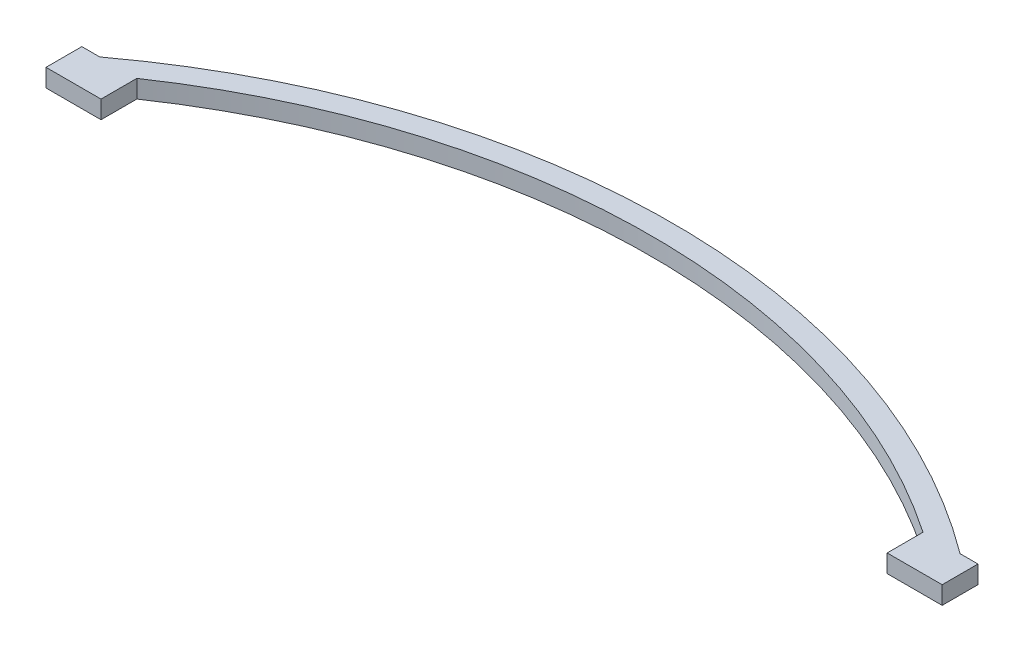
SolidWorks part; units mm, degrees
ref_plane "Front" through (0, 0, 0) normal (0, 0, 1) x (1, 0, 0)
ref_plane "Top" through (0, 0, 0) normal (0, 1, 0) x (1, 0, 0)
ref_plane "Right" through (0, 0, 0) normal (1, 0, 0) x (0, 0, -1)
sketch "Sketch1" plane through (0, 0, 0) normal (0, 1, 0) x (1, 0, 0)
  line L0 (-76.2, 0) -> (76.2, 0) construction
  line L1 (0, 0) -> (0, 25.24) construction
  line L2 (-76.2, 0) -> (-69.6298, 0)
  line L3 (69.6298, 0) -> (76.2, 0)
  arc A0 (-76.2, 0) -> (76.2, 0) centre (0, -102.4046) cw
  arc A1 (-69.6298, 0) -> (69.6298, 0) centre (0, -102.4046) cw
  arc A2 (-73.9255, -3.0566) -> (73.9255, -3.0566) centre (0, -102.4046) cw construction
  point P4 (0, 0)
  dimension "D1" = 152.4
  dimension "D2" = 25.24
  dimension "D3" = 3.81
extrude "Boss-Extrude2" add sketch "Sketch1" along normal blind 3.175
sketch "Sketch2" plane through (0, 0, 0) normal (0, 0, 1) x (1, 0, 0)
  line L0 (-76.2, 3.175) -> (-76.2, 0) construction
  line L1 (-69.6298, 3.175) -> (-79.375, 3.175)
  line L2 (-69.6298, 3.175) -> (-69.6298, 0)
  line L3 (-69.6298, 0) -> (-79.375, 0)
  line L4 (-79.375, 3.175) -> (-79.375, 0)
  line L5 (0, 98.156) -> (0, -98.156) construction
  line L7 (69.6298, 0) -> (79.375, 0)
  line L8 (79.375, 3.175) -> (79.375, 0)
  line L9 (69.6298, 3.175) -> (79.375, 3.175)
  line L10 (69.6298, 3.175) -> (69.6298, 0)
  point P11 (0, 0)
  dimension "D1" = 3.175
  dimension "D2" = 3.175
extrude "Boss-Extrude3" add sketch "Sketch2" along normal blind 6.35
